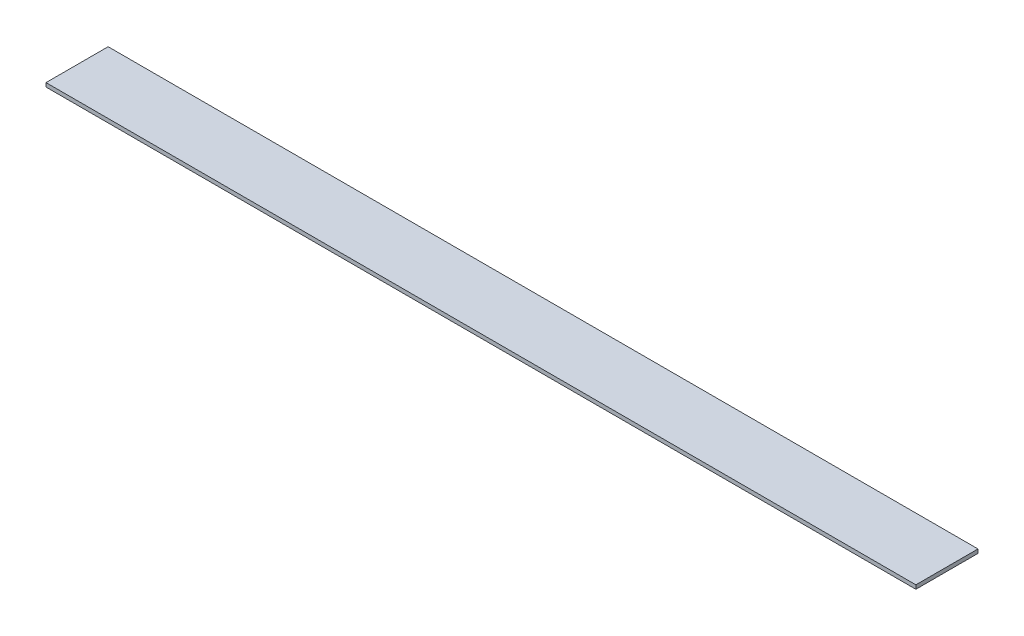
SolidWorks part; units mm, degrees
ref_plane "Front Plane" through (0, 0, 0) normal (0, 0, 1) x (1, 0, 0)
ref_plane "Top Plane" through (0, 0, 0) normal (0, 1, 0) x (1, 0, 0)
ref_plane "Right Plane" through (0, 0, 0) normal (1, 0, 0) x (0, 0, -1)
sketch "Sketch1" plane through (0, 0, 0) normal (0, 1, 0) x (1, 0, 0)
  line L1 (0, 0) -> (355.6, 0)
  line L2 (0, 0) -> (0, 25.4)
  line L3 (0, 25.4) -> (355.6, 25.4)
  line L4 (355.6, 0) -> (355.6, 25.4)
  dimension "D1" = 25.4
  dimension "D2" = 355.6
extrude "Boss-Extrude1" add sketch "Sketch1" along normal blind 1.5875
